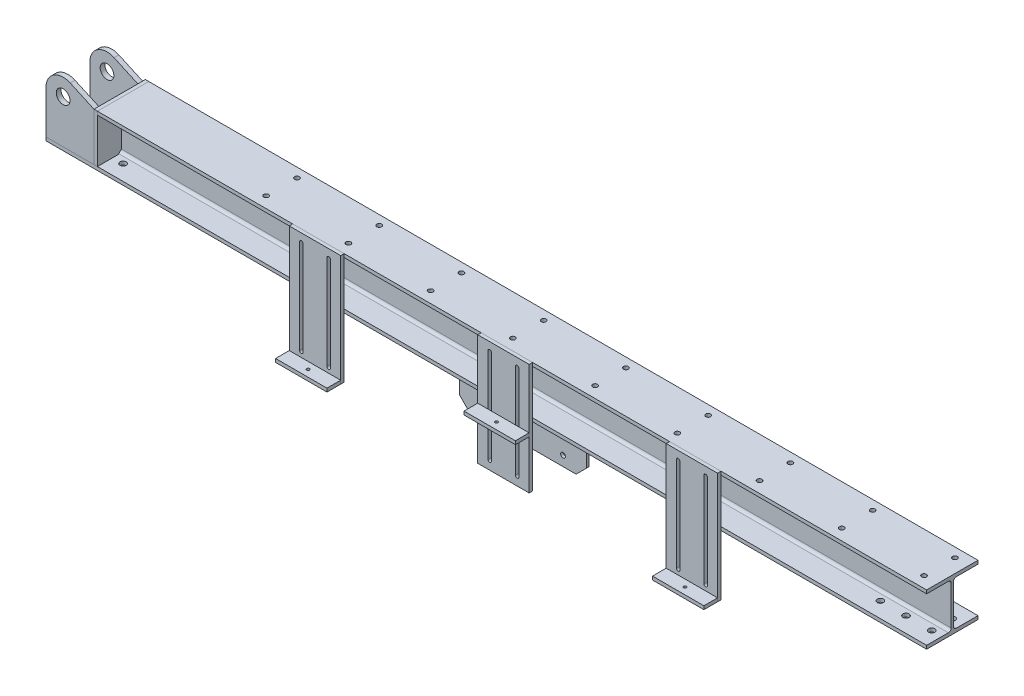
SolidWorks part; units mm, degrees
material "普通碳钢"
ref_plane "前视基准面" through (0, 0, 0) normal (0, 0, 1) x (1, 0, 0)
ref_plane "上视基准面" through (0, 0, 0) normal (0, 1, 0) x (1, 0, 0)
ref_plane "右视基准面" through (0, 0, 0) normal (1, 0, 0) x (0, 0, -1)
sketch "草图15" plane through (0, 0, 0) normal (0, 1, 0) x (1, 0, 0)
  line L0 (0, 0) -> (2570, 0)
  dimension "D1" = 2570
other "H型钢 HW150(1)"
ref_plane "基准面8" through (0, 0, 0) normal (1, 0, 0) x (0, 0, -1)
sketch "草图111" plane through (0, 0, 0) normal (1, 0, 0) x (0, 0, -1)
  line L0 (-75, -75) -> (75, -75)
  line L1 (75, -75) -> (75, -65)
  line L2 (75, -65) -> (11.5, -65)
  line L3 (3.5, -57) -> (3.5, 57)
  line L4 (11.5, 65) -> (75, 65)
  line L5 (75, 65) -> (75, 75)
  line L6 (75, 75) -> (-75, 75)
  line L7 (0, 75) -> (0, -75) construction
  line L11 (0, 60) -> (0, 75) construction
  line L14 (-75, -75) -> (-75, -65)
  line L15 (-75, -65) -> (-11.5, -65)
  line L16 (-3.5, -57) -> (-3.5, 57)
  line L17 (-11.5, 65) -> (-75, 65)
  line L18 (-75, 65) -> (-75, 75)
  arc A2 (11.5, -65) -> (3.5, -57) centre (11.5, -57) cw
  arc A3 (3.5, 57) -> (11.5, 65) centre (11.5, 57) cw
  arc A5 (-11.5, -65) -> (-3.5, -57) centre (-11.5, -57) ccw
  arc A6 (-3.5, 57) -> (-11.5, 65) centre (-11.5, 57) ccw
  point P2 (0, 0)
  point P38 (0, 0)
  point P39 (75, 75)
  point P40 (75, -75)
  point P41 (-75, -75)
  dimension "D8" = 8
  dimension "D1" = 7
  dimension "D2" = 10
  dimension "D3" = 150
  dimension "D4" = 150
  dimension "D9" = 0
ref_plane "基准面9" through (75, 0, 0) normal (-1, 0, 0) x (0, 0, 1)
sketch "草图18" plane through (0, -75, 0) normal (0, -1, 0) x (1, 0, 0)
  line L0 (0, 0) -> (2570, 0) construction
  line L2 (0, -30) -> (2570, -30) construction
  line L3 (0, 30) -> (2570, 30) construction
  line L6 (2540, 75) -> (2540, -75)
  line L7 (2540, 75) -> (2540, -75) construction
  line L8 (105, 75) -> (105, -75) construction
  line L9 (30, 75) -> (30, -75)
  line L10 (30, 75) -> (30, -75) construction
  line L11 (180, 75) -> (180, -75) construction
  line L12 (2465, 75) -> (2465, -75) construction
  line L13 (2390, 75) -> (2390, -75) construction
  circle A0 centre (30, 30) radius 9
  circle A1 centre (30, -30) radius 9
  circle A2 centre (105, -30) radius 9
  circle A3 centre (105, 30) radius 9
  circle A4 centre (180, 30) radius 9
  circle A5 centre (180, -30) radius 9
  circle A6 centre (2390, 30) radius 9
  circle A7 centre (2465, 30) radius 9
  circle A8 centre (2540, 30) radius 9
  circle A9 centre (2540, -30) radius 9
  circle A10 centre (2465, -30) radius 9
  circle A11 centre (2390, -30) radius 9
  dimension "D9" = 18
  dimension "D1" = 30
  dimension "D2" = 30
  dimension "D3" = 30
  dimension "D4" = 30
  dimension "D5" = 75
  dimension "D6" = 75
  dimension "D7" = 75
  dimension "D8" = 75
extrude "切除-拉伸2" cut sketch "草图18" against normal up to next
sketch "草图19" plane through (0, -75, 0) normal (0, -1, 0) x (1, 0, 0)
  line L0 (2570, -75) -> (2570, -11.5) construction
  line L1 (1136, 4) -> (1506, 4)
  line L2 (1136, 4) -> (1136, -4)
  line L3 (1136, -4) -> (1506, -4)
  line L4 (1506, 4) -> (1506, -4)
  line L5 (0, 0) -> (2570, 0) construction
  line L6 (1321, 50) -> (1321, -50) construction
  dimension "D1" = 370
  dimension "D2" = 8
  dimension "D3" = 1249
extrude "凸台-拉伸3" add sketch "草图19" along normal blind 140 separate body
chamfer "倒角1" distance 30 angle 45 2 edges at (1506, -215, 0) (1136, -215, 0)
sketch "草图20" plane through (0, 0, -4) normal (0, 0, -1) x (-1, 0, 0)
  line L0 (-1778.4873, -840.1463) -> (-1380.1773, -75) construction
  line L1 (-1506, -75) -> (-1136, -75) construction
  line L2 (-1506, -185) -> (-1506, -75) construction
  line L3 (-1136, -185) -> (-1136, -75) construction
  line L4 (-1136, -75) -> (-1506, -75) construction
  line L5 (-1321, -75) -> (-1321, -215) construction
  line L6 (-1166, -215) -> (-1476, -215) construction
  line L7 (-1401, -75) -> (-1401, -215) construction
  line L9 (-1401, -115) -> (-1364.0356, -134.2424) construction
  line L10 (-1241, -115) -> (-1277.9644, -134.2424) construction
  line L12 (-1241, -75) -> (-1241, -215) construction
  line L13 (-863.5127, -840.1463) -> (-1261.8227, -75) construction
  circle A1 centre (-1401, -115) radius 7
  circle A2 centre (-1241, -115) radius 7
  circle A4 centre (-1437.9399, -185.9609) radius 7
  circle A5 centre (-1204.0601, -185.9609) radius 7
  dimension "D5" = 14
  dimension "D6" = 14
  dimension "D7" = 80
  dimension "D4" = 14
  dimension "D1" = 80
  dimension "D2" = 27.5
  dimension "D3" = 40
  dimension "D8" = 80
extrude "切除-拉伸3" cut sketch "草图20" against normal up to next (8 mm away)
sketch "草图112" plane through (0, 0, 0) normal (0, 0, 1) x (1, 0, 0)
  line L0 (0, 75) -> (150, 75)
  line L1 (2570, 75) -> (0, 75) construction
  line L2 (150, 75) -> (150, 60)
  line L3 (150, 60) -> (10, -65)
  line L4 (2570, -65) -> (0, -65) construction
  line L5 (10, -65) -> (0, -65)
  line L6 (0, -57) -> (0, -65) construction
  line L7 (0, -65) -> (0, 75)
  dimension "D1" = 10
  dimension "D2" = 15
  dimension "D3" = 150
extrude "切除-拉伸4" cut sketch "草图112" against normal mid plane 150
sketch "草图113" plane through (150, 0, 0) normal (-1, 0, 0) x (0, 0, 1)
  line L0 (75, 65) -> (75, 75) construction
  line L1 (-75, 75) -> (75, 75)
  line L2 (-75, 75) -> (-75, -65)
  line L3 (-75, -65) -> (-14, -65)
  line L4 (75, 75) -> (75, -65)
  line L5 (-75, -65) -> (75, -65) construction
  line L6 (-4, -55) -> (-4, 60.5)
  line L13 (-4.0838, 60.5) -> (4.0838, 60.5)
  line L14 (-4, 60.5) -> (4, 60.5)
  line L20 (4, 60.5) -> (4, -55)
  line L22 (14, -65) -> (75, -65)
  line L23 (-14, -65) -> (-4, -55)
  line L24 (4, -55) -> (14, -65)
  point P9 (-4, -65)
  point P12 (4, -65)
  dimension "D1" = 71
  dimension "D2" = 0.5
  dimension "D3" = 71
extrude "凸台-拉伸4" add sketch "草图113" along normal blind 10 separate body
ref_plane "基准面10" through (0, 0, -67) normal (0, 0, -1) x (-1, 0, 0)
sketch "草图114" plane through (0, 0, 75) normal (0, 0, 1) x (1, 0, 0)
  line L0 (0, -65) -> (0, 61)
  line L1 (2570, -65) -> (0, -65) construction
  line L2 (140, 75) -> (70.6977, 106.5149)
  line L3 (140, 75) -> (140, -65)
  line L4 (140, -65) -> (0, -65)
  arc A0 (70.6977, 106.5149) -> (0, 61) centre (50, 61) ccw
  dimension "D1" = 100
  dimension "D2" = 126
extrude "凸台-拉伸5" add sketch "草图114" against normal blind 14 separate body
sketch "草图115" plane through (0, 0, -67) normal (0, 0, -1) x (-1, 0, 0)
  line L4 (-140, -65) -> (0, -65)
  line L5 (0, -65) -> (0, 61)
  line L6 (-70.6977, 106.5149) -> (-140, 75)
  line L7 (-140, 75) -> (-140, -65)
  line L8 (-140, -65) -> (0, -65)
  line L9 (0, -65) -> (0, 61)
  line L10 (-70.6977, 106.5149) -> (-140, 75)
  line L11 (-140, 75) -> (-140, -65)
  arc A1 (0, 61) -> (-70.6977, 106.5149) centre (-50, 61) ccw
  arc A2 (0, 61) -> (-70.6977, 106.5149) centre (-50, 61) ccw
  dimension "D1" = 0
extrude "凸台-拉伸6" add sketch "草图115" against normal blind 14 separate body
sketch "草图116" plane through (0, 0, 75) normal (0, 0, 1) x (1, 0, 0)
  line L0 (2570, -75) -> (0, -75) construction
  line L1 (0, 61) -> (0, -65) construction
  circle A0 centre (50, 61.5) radius 20
  dimension "D1" = 40
  dimension "D2" = 136.5
  dimension "D3" = 50
extrude "切除-拉伸5" cut sketch "草图116" against normal up to next (14 mm away)
sketch "草图117" plane through (0, 0, -67) normal (0, 0, -1) x (-1, 0, 0)
  circle A0 centre (-50, 61) radius 20
  dimension "D1" = 40
extrude "切除-拉伸6" cut sketch "草图117" against normal up to next (14 mm away)
ref_plane "基准面11" through (2420, 0, 0) normal (1, 0, 0) x (0, 0, -1)
sketch "草图118" plane through (2420, 0, 0) normal (1, 0, 0) x (0, 0, -1)
  line L0 (11.5, 65) -> (75, 65) construction
  line L1 (13.5, 65) -> (73.5, 65)
  line L2 (3.5, -57) -> (3.5, 57) construction
  line L3 (3.5, -55) -> (3.5, 55)
  line L4 (75, -65) -> (11.5, -65) construction
  line L5 (73.5, -65) -> (13.5, -65)
  line L6 (3.5, 55) -> (13.5, 65)
  line L7 (13.5, -65) -> (3.5, -55)
  line L9 (73.5, -65) -> (73.5, 65)
  point P8 (3.5, 65)
  point P11 (3.5, -65)
  dimension "D1" = 70
extrude "凸台-拉伸7" add sketch "草图118" along normal blind 6 separate body
pattern_linear "阵列(线性)1" count 4 spacing 570 along (-1, 0, 0) of "凸台-拉伸7"
sketch "草图119" plane through (0, 75, 0) normal (0, 1, 0) x (1, 0, 0)
  line L0 (2530, 47.5) -> (2530, -42.5) construction
  line L1 (2570, 75) -> (2570, -75) construction
  line L2 (2570, 75) -> (150, 75) construction
  line L3 (2290, 47.5) -> (2290, -42.5) construction
  line L4 (2050, 47.5) -> (2050, -42.5) construction
  line L5 (1810, 47.5) -> (1810, -42.5) construction
  line L6 (1570, 47.5) -> (1570, -42.5) construction
  line L7 (1330, 47.5) -> (1330, -42.5) construction
  line L8 (1090, 47.5) -> (1090, -42.5) construction
  line L9 (850, 47.5) -> (850, -42.5) construction
  line L10 (610, 47.5) -> (610, -42.5) construction
  circle A0 centre (2530, -42.5) radius 7
  circle A1 centre (2530, 47.5) radius 7
  circle A2 centre (2290, -42.5) radius 7
  circle A3 centre (2290, 47.5) radius 7
  circle A4 centre (2050, -42.5) radius 7
  circle A5 centre (2050, 47.5) radius 7
  circle A6 centre (1810, -42.5) radius 7
  circle A7 centre (1810, 47.5) radius 7
  circle A8 centre (1570, -42.5) radius 7
  circle A9 centre (1570, 47.5) radius 7
  circle A10 centre (1330, -42.5) radius 7
  circle A11 centre (1330, 47.5) radius 7
  circle A12 centre (1090, -42.5) radius 7
  circle A13 centre (1090, 47.5) radius 7
  circle A14 centre (850, -42.5) radius 7
  circle A15 centre (850, 47.5) radius 7
  circle A16 centre (610, -42.5) radius 7
  circle A17 centre (610, 47.5) radius 7
  point P6 (2290, 2.5)
  dimension "D1" = 14
  dimension "D2" = 14
  dimension "D3" = 90
  dimension "D4" = 40
  dimension "D5" = 27.5
  dimension "D7" = 240
  dimension "D6" = 9
extrude "切除-拉伸7" cut sketch "草图119" against normal up to next (10 mm away)
sketch "草图120" plane through (0, 0, 75) normal (0, 0, 1) x (1, 0, 0)
  line L0 (2570, 75) -> (150, 75) construction
  line L1 (1820, 75) -> (1970, 75)
  line L2 (1820, 75) -> (1820, -250)
  line L3 (1820, -250) -> (1970, -250)
  line L4 (1970, 75) -> (1970, -250)
  line L5 (2570, -75) -> (0, -75) construction
  line L6 (2570, 75) -> (2570, 65) construction
  line L7 (1855, 75) -> (1855, -250) construction
  line L8 (1935, 75) -> (1935, -250) construction
  line L9 (1820, 50) -> (1970, 50) construction
  line L10 (1820, -225) -> (1970, -225) construction
  line L11 (2570, 65) -> (150, 65) construction
  line L12 (1850, -225) -> (1850, 50)
  line L13 (1860, 50) -> (1860, -225)
  line L14 (1930, 50) -> (1930, -225)
  line L15 (1940, 50) -> (1940, -225)
  arc A0 (1860, 50) -> (1850, 50) centre (1855, 50) ccw
  arc A1 (1940, 50) -> (1930, 50) centre (1935, 50) ccw
  arc A2 (1850, -225) -> (1860, -225) centre (1855, -225) ccw
  arc A3 (1930, -225) -> (1940, -225) centre (1935, -225) ccw
  dimension "D8" = 10
  dimension "D1" = 175
  dimension "D2" = 150
  dimension "D3" = 600
  dimension "D4" = 25
  dimension "D5" = 15
  dimension "D6" = 35
  dimension "D7" = 35
extrude "凸台-拉伸8" add sketch "草图120" along normal blind 10 separate body
pattern_linear "阵列(线性)2" count 3 spacing 550 along (-1, 0, 0) of "凸台-拉伸8"
sketch "草图121" plane through (0, 0, 85) normal (0, 0, 1) x (1, 0, 0)
  line L0 (720, 75) -> (720, -250) construction
  line L1 (720, -240) -> (870, -240)
  line L2 (720, -240) -> (720, -250)
  line L3 (720, -250) -> (870, -250)
  line L4 (870, -240) -> (870, -250)
  line L5 (870, -250) -> (870, 75) construction
  dimension "D1" = 10
extrude "凸台-拉伸9" add sketch "草图121" along normal blind 40 separate body
sketch "草图122" plane through (0, 0, 85) normal (0, 0, 1) x (1, 0, 0)
  line L0 (1420, -250) -> (1420, 75) construction
  line L1 (1270, -108) -> (1420, -108)
  line L2 (1270, -108) -> (1270, -98)
  line L3 (1270, -98) -> (1420, -98)
  line L4 (1420, -108) -> (1420, -98)
  line L6 (1270, -250) -> (1420, -250) construction
  dimension "D1" = 10
  dimension "D2" = 142
extrude "凸台-拉伸10" add sketch "草图122" along normal blind 40 separate body
sketch "草图123" plane through (0, 0, 85) normal (0, 0, 1) x (1, 0, 0)
  line L0 (1820, 75) -> (1820, -250) construction
  line L1 (1820, -240) -> (1970, -240)
  line L2 (1820, -240) -> (1820, -250)
  line L3 (1820, -250) -> (1970, -250)
  line L4 (1970, -240) -> (1970, -250)
  line L5 (1970, -250) -> (1970, 75) construction
  line L7 (1820, -250) -> (1970, -250) construction
  dimension "D1" = 10
extrude "凸台-拉伸11" add sketch "草图123" along normal blind 40 separate body
ref_plane "基准面12" through (795, 0, 0) normal (-1, 0, 0) x (0, 0, 1)
sketch "草图124" plane through (795, 0, 0) normal (-1, 0, 0) x (0, 0, 1)
  line L0 (65, -75) -> (75, -85)
  line L2 (75, -85) -> (75, -250)
  line L3 (75, -250) -> (65, -250)
  line L4 (65, -250) -> (4, -95)
  line L5 (4, -185) -> (4, -75) construction
  line L6 (4, -95) -> (4, -85)
  line L7 (4, -85) -> (14, -75)
  line L8 (14, -75) -> (65, -75)
  line L9 (75, -75) -> (-75, -75) construction
  dimension "D1" = 10
  dimension "D2" = 10
  dimension "D3" = 10
  dimension "D4" = 10
  dimension "D5" = 10
extrude "凸台-拉伸12" add sketch "草图124" along normal mid plane 6 separate body
pattern_linear "阵列(线性)3" count 3 spacing 550 along (1, 0, 0) of "凸台-拉伸12"
hole_wizard "M10 螺纹孔1" positions "3D草图1" profile "草图125" tap size "M10" standard "GB" end condition up to next
sketch3d "3D草图1"
  line L0 (1270, -108, 125) -> (1420, -108, 125) construction
  line L1 (1420, -108, 125) -> (1420, -108, 85) construction
  point P0 (1345, -108, 105)
  dimension "D1" = 20
  dimension "D2" = 75
sketch "草图125" plane through (1345, -108, 105) normal (1, 0, 0) x (0, 0, -1)
  line L0 (0, 0) -> (0, 10.001)
  line L1 (0, 10.001) -> (4.25, 10.001)
  line L2 (4.25, 10.001) -> (4.25, 0)
  line L5 (4.25, 0) -> (0, 0)
  line L11 (0, -6.35) -> (0, 107.95) construction
  dimension "通孔螺纹孔钻头直径" = 8.5
  dimension "通孔螺纹孔钻头深度" = 10.001
cosmetic thread "孔螺蚊线1" parameters "D2"=10
hole_wizard "M10 螺纹孔2" positions "3D草图2" profile "草图126" tap size "M10" standard "GB" end condition up to next
sketch3d "3D草图2"
  line L0 (870, -240, 125) -> (720, -240, 125) construction
  line L1 (720, -240, 125) -> (720, -240, 85) construction
  line L2 (1970, -240, 125) -> (1820, -240, 125) construction
  line L3 (1820, -240, 125) -> (1820, -240, 85) construction
  point P0 (795, -240, 105)
  point P2 (1895, -240, 105)
  dimension "D1" = 20
  dimension "D2" = 75
  dimension "D3" = 20
  dimension "D4" = 75
sketch "草图126" plane through (795, -240, 105) normal (1, 0, 0) x (0, 0, 1)
  line L0 (0, 0) -> (0, 10.001)
  line L1 (0, 10.001) -> (4.25, 10.001)
  line L2 (4.25, 10.001) -> (4.25, 0)
  line L5 (4.25, 0) -> (0, 0)
  line L11 (0, -6.35) -> (0, 107.95) construction
  dimension "通孔螺纹孔钻头直径" = 8.5
  dimension "通孔螺纹孔钻头深度" = 10.001
cosmetic thread "孔螺蚊线2" parameters "D2"=10
cosmetic thread "孔螺蚊线3" parameters "D2"=10
